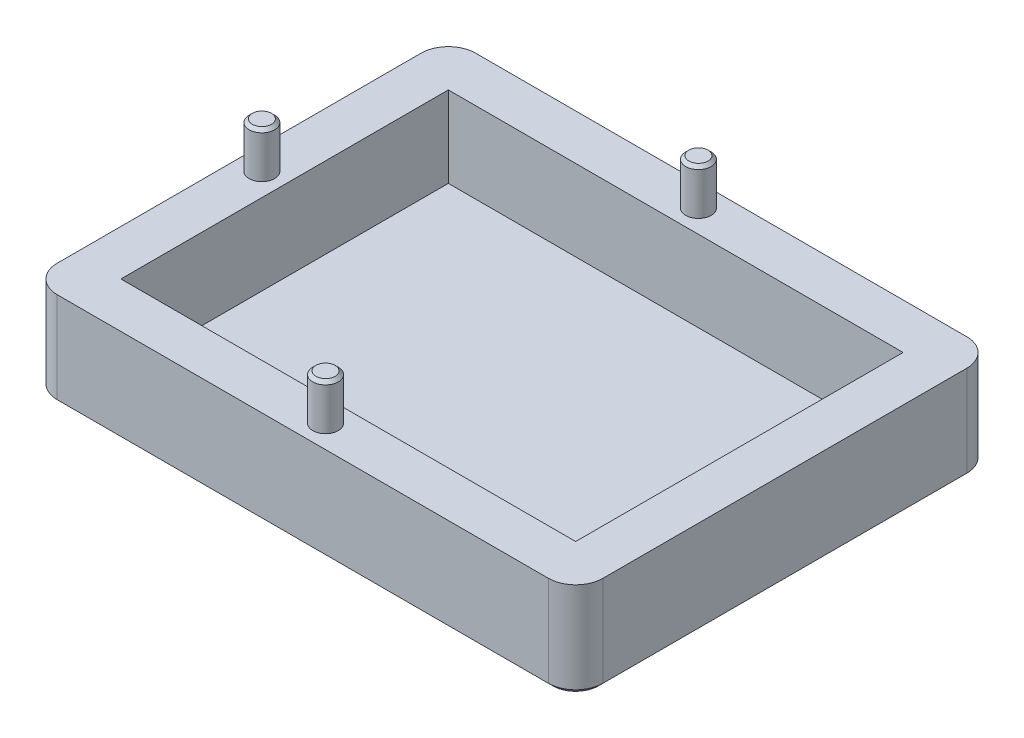
SolidWorks part; units mm, degrees
ref_plane "Front Plane" through (0, 0, 0) normal (0, 0, 1) x (1, 0, 0)
ref_plane "Top Plane" through (0, 0, 0) normal (0, 1, 0) x (1, 0, 0)
ref_plane "Right Plane" through (0, 0, 0) normal (1, 0, 0) x (0, 0, -1)
sketch "Sketch1" plane through (0, 0, 0) normal (0, 1, 0) x (1, 0, 0)
  line L0 (-5, 41) -> (55, 41)
  line L1 (0, 0) -> (50, 0)
  line L2 (0, 0) -> (0, 36)
  line L3 (0, 36) -> (50, 36)
  line L4 (50, 0) -> (50, 36)
  line L5 (55, -5) -> (55, 41)
  line L6 (-5, -5) -> (55, -5)
  line L7 (-5, -5) -> (-5, 41)
  dimension "D1" = 50
  dimension "D2" = 36
  dimension "D3" = 5
extrude "Boss-Extrude1" add sketch "Sketch1" along normal blind 10.5
sketch "Sketch2" plane through (0, 0, 0) normal (0, 1, 0) x (1, 0, 0)
  line L1 (0, 36) -> (50, 36)
  line L2 (0, 36) -> (0, 0)
  line L3 (0, 0) -> (50, 0)
  line L4 (50, 36) -> (50, 0)
extrude "Boss-Extrude2" add sketch "Sketch2" along normal blind 1.6
fillet "Fillet1" radius 3 4 edges at (55, 5.25, -41) (-5, 5.25, -41) (55, 5.25, 5) (-5, 5.25, 5)
sketch "Sketch3" plane through (0, 10.5, 0) normal (0, 1, 0) x (1, 0, 0)
  line L0 (25, 41) -> (25, -5) construction
  line L1 (52, 41) -> (-2, 41) construction
  line L2 (-2, -5) -> (52, -5) construction
  line L3 (25, 18) -> (-5, 18) construction
  line L4 (-5, 38) -> (-5, -2) construction
  circle A0 centre (25, 38.5) radius 1.4
  circle A1 centre (-2.5, 18) radius 1.4
  circle A2 centre (25, -2.5) radius 1.4
  dimension "D1" = 2.8
  dimension "D3" = 2.8
  dimension "D2" = 2.5
  dimension "D4" = 2.5
extrude "Boss-Extrude3" add sketch "Sketch3" along normal blind 5
chamfer "Chamfer1" distance 0.35 angle 45 3 edges at (25, 15.5, 1.1) (-2.5, 15.5, -16.6) (25, 15.5, -37.1)
chamfer "Chamfer2" distance 0.5 angle 45 8 edges at (-4.1213, 0, -40.1213) (-5, 0, -18) (-4.1213, 0, 4.1213) (25, 0, 5) (54.1213, 0, 4.1213) (55, 0, -18) (54.1213, 0, -40.1213) (25, 0, -41)
